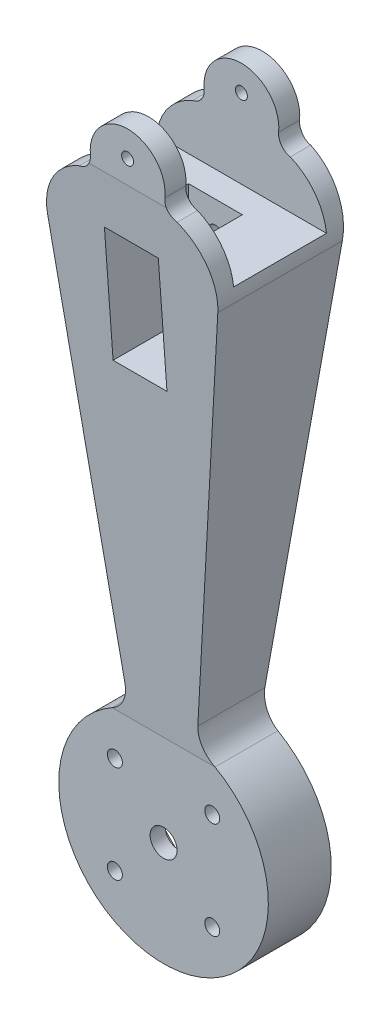
SolidWorks part; units mm, degrees
ref_plane "Front Plane" through (0, 0, 0) normal (0, 0, 1) x (1, 0, 0)
ref_plane "Top Plane" through (0, 0, 0) normal (0, 1, 0) x (1, 0, 0)
ref_plane "Right Plane" through (0, 0, 0) normal (1, 0, 0) x (0, 0, -1)
sketch "Sketch1" plane through (0, 0, 0) normal (0, 0, 1) x (1, 0, 0)
  line L0 (0, 200) -> (0, 0) construction
  line L1 (-12.1376, 40.1302) -> (-28.4146, 172.6959)
  line L2 (12.1376, 40.1302) -> (28.4146, 172.6959)
  arc A0 (-17.1846, 30.4908) -> (17.1846, 30.4908) centre (0, 0) ccw
  arc A1 (12.4372, 198.7481) -> (-12.4372, 198.7481) centre (0, 200) ccw
  arc A2 (-28.4146, 172.6959) -> (-16.3316, 193.5631) centre (-8.5637, 175.1333) cw
  arc A4 (28.4146, 172.6959) -> (16.3316, 193.5631) centre (8.5637, 175.1333) ccw
  arc A6 (-16.3316, 193.5631) -> (-12.4372, 198.7481) centre (-17.198, 198.2689) ccw
  arc A7 (16.3316, 193.5631) -> (12.4372, 198.7481) centre (17.198, 198.2689) cw
  arc A8 (-12.1376, 40.1302) -> (-17.1846, 30.4908) centre (-22.0945, 39.2025) cw
  arc A9 (12.1376, 40.1302) -> (17.1846, 30.4908) centre (22.0945, 39.2025) ccw
  dimension "D1" = 70
  dimension "D2" = 25
  dimension "D5" = 20
  dimension "D3" = 200
  dimension "D6" = 7
extrude "Boss-Extrude1" add sketch "Sketch1" along normal blind 45
sketch "Sketch4" plane through (0, 0, 0) normal (1, 0, 0) x (0, 0, -1)
  line L0 (-22.5, 212.5) -> (-22.5, -35) construction
  line L1 (0, 212.5) -> (-45, 212.5) construction
  line L2 (-45, -35) -> (0, -35) construction
  line L3 (-45, 196.1556) -> (-33, 30.4908)
  line L4 (-45, 198.7481) -> (-45, 193.5631) construction
  line L5 (-45, 30.4908) -> (0, 30.4908) construction
  line L6 (-33, 30.4908) -> (-33, -35)
  line L7 (-33, -35) -> (-45, -35)
  line L8 (-45, -35) -> (-45, 196.1556)
  line L9 (-12, -35) -> (0, -35)
  line L10 (-12, 30.4908) -> (-12, -35)
  line L11 (0, 196.1556) -> (-12, 30.4908)
  line L12 (0, -35) -> (0, 196.1556)
  dimension "D1" = 10.5
extrude "Cut-Extrude2" cut sketch "Sketch4" against normal through all both and the other way through all
sketch "Sketch5" plane through (0, 0, 0) normal (0, 0, 1) x (1, 0, 0)
  line L1 (16.97, -20.5) -> (-16.97, -20.5)
  line L2 (20.5, -16.97) -> (20.5, 16.97)
  line L3 (16.97, 20.5) -> (-16.97, 20.5)
  line L4 (-20.5, -16.97) -> (-20.5, 16.97)
  line L5 (18.735, -18.735) -> (-20.5, 20.5) construction
  line L6 (20.5, 20.5) -> (-20.5, -20.5) construction
  line L7 (-16.97, 20.5) -> (-20.5, 16.97)
  line L10 (16.97, 20.5) -> (20.5, 16.97)
  line L13 (-20.5, -16.97) -> (-16.97, -20.5)
  line L16 (20.5, -16.97) -> (16.97, -20.5)
  point P0 (0, 0)
  dimension "D1" = 41
  dimension "D3" = 3.53
  dimension "D4" = 3.53
  dimension "D5" = 3.53
  dimension "D6" = 3.53
  dimension "D9" = 3.53
extrude "Cut-Extrude3" cut sketch "Sketch5" along normal blind 28
sketch "Sketch6" plane through (0, 0, 28) normal (0, 0, -1) x (-1, 0, 0)
  line L0 (-18.735, 18.735) -> (18.735, -18.735) construction
  line L1 (-20.5, 16.97) -> (-16.97, 20.5) construction
  line L2 (20.5, -16.97) -> (16.97, -20.5) construction
  line L3 (18.735, 18.735) -> (-18.735, -18.735) construction
  line L4 (20.5, 16.97) -> (16.97, 20.5) construction
  line L5 (-20.5, -16.97) -> (-16.97, -20.5) construction
  circle A0 centre (0, 0) radius 4.5
  circle A1 centre (-16.2574, 16.2574) radius 2.5
  circle A2 centre (16.2601, 16.2601) radius 2.5
  circle A3 centre (-16.2601, -16.2601) radius 2.5
  circle A4 centre (16.2601, -16.2601) radius 2.5
  dimension "D1" = 9
  dimension "D2" = 5
  dimension "D3" = 5
  dimension "D5" = 5
  dimension "D6" = 5
  dimension "D4" = 3.5039
  dimension "D7" = 3.5
  dimension "D8" = 3.5
  dimension "D9" = 3.5
extrude "Cut-Extrude4" cut sketch "Sketch6" against normal through all both and the other way through all
sketch "Sketch7" plane through (7.1032, -0.8722, 0) normal (0.9925, -0.1219, 0) x (0, 0, -1)
  line L0 (-37.8122, 211.0092) -> (-37.8122, 194.1106)
  line L1 (0, 211.0092) -> (-45, 211.0092) construction
  line L2 (-44.8122, 194.1106) -> (-0.1878, 194.1106) construction
  line L3 (-37.8122, 194.1106) -> (-7.1878, 194.1106)
  line L4 (-7.1878, 194.1106) -> (-7.1878, 211.0092)
  line L5 (-7.1878, 211.0092) -> (-37.8122, 211.0092)
  dimension "D1" = 7
  dimension "D2" = 7
sketch "Sketch8" plane through (0, 1.0238, 14.1345) normal (0, -0.0722, -0.9974) x (-1, 0, 0)
  line L0 (-2.8845, 56.793) -> (-14.8249, 154.294)
  line L1 (3.2141, 56.6687) -> (15.1696, 154.294)
  line L2 (-23.1018, 128.7389) -> (-18.4336, 90.6195) construction
  line L3 (-12.1376, 39.2088) -> (-28.4146, 172.1218) construction
  line L4 (0, 211.9447) -> (0, 41.9008) construction
  line L5 (23.8053, 134.4833) -> (18.7044, 92.8308) construction
  line L6 (28.4146, 172.1218) -> (12.1376, 39.2088) construction
  arc A0 (-14.8249, 154.294) -> (15.1696, 154.294) centre (0.1724, 149.3565) cw
  arc A1 (-2.8845, 56.793) -> (3.2141, 56.6687) centre (0.1532, 56.1602) ccw
  ellipse E0 centre (0, 199.4774) end of major axis (-12.5, 199.4774) minor radius 12.4673 (12.4372, 198.2288) -> (-12.4372, 198.2288) ccw construction
extrude "Cut-Extrude6" cut sketch "Sketch8" along direction (0, 0.0722, -0.9974) on the side against the normal blind 10
sketch "Sketch12" plane through (0, 0, 0) normal (1, 0, 0) x (0, 0, -1)
  line L1 (-48.6765, 138.9907) -> (-15.6765, 138.9907)
  line L2 (-48.6765, 138.9907) -> (-48.6765, 178.9907)
  line L3 (-48.6765, 178.9907) -> (-15.6765, 178.9907)
  line L4 (-15.6765, 138.9907) -> (-15.6765, 178.9907)
  line L5 (-48.6765, 138.9907) -> (-15.6765, 178.9907) construction
  line L6 (-48.6765, 178.9907) -> (-15.6765, 138.9907) construction
  point P0 (-32.1765, 158.9907)
  dimension "D1" = 40
  dimension "D2" = 33
extrude "Cut-Extrude9" cut sketch "Sketch12" against normal blind 9 and the other way blind 9
sketch "Sketch13" plane through (0, 0, 0) normal (1, 0, 0) x (0, 0, -1)
  line L0 (0, 212.5) -> (-45, 212.5) construction
  line L1 (-38, 212.5) -> (-7, 212.5)
  line L2 (-38, 212.5) -> (-38, 177.5)
  line L3 (-38, 177.5) -> (-7, 177.5)
  line L4 (-7, 212.5) -> (-7, 177.5)
  line L5 (-45, 212.5) -> (-45, 198.7481) construction
  dimension "D1" = 35
  dimension "D2" = 7
  dimension "D3" = 7
extrude "Cut-Extrude10" cut sketch "Sketch13" against normal through all both and the other way through all
sketch "Sketch14" plane through (0, 0, 0) normal (0, 0, 1) x (1, 0, 0)
  circle A0 centre (0, 203.8964) radius 2
  dimension "D1" = 4
extrude "Cut-Extrude13" cut sketch "Sketch14" against normal blind 9 and the other way through all
sketch "Sketch15" plane through (0, 0, 15.6765) normal (0, 0, 1) x (1, 0, 0)
  line L0 (-28.4232, 177.5) -> (28.4232, 177.5) construction
  circle A0 centre (0, 167.5) radius 2.5
  point P4 (0, 177.5)
  dimension "D2" = 5
  dimension "D1" = 10
extrude "Cut-Extrude14" cut sketch "Sketch15" against normal through all
